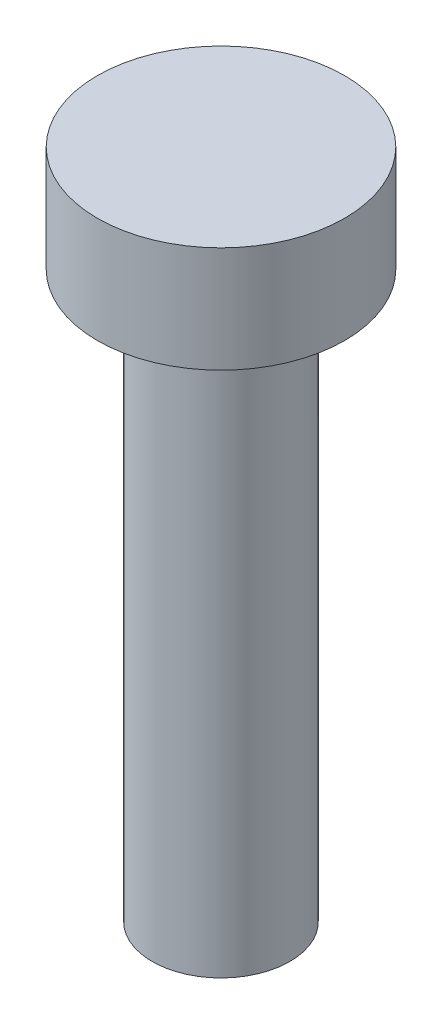
SolidWorks part; units mm, degrees
ref_plane "Front Plane" through (0, 0, 0) normal (0, 0, 1) x (1, 0, 0)
ref_plane "Top Plane" through (0, 0, 0) normal (0, 1, 0) x (1, 0, 0)
ref_plane "Right Plane" through (0, 0, 0) normal (1, 0, 0) x (0, 0, -1)
sketch "Sketch1" plane through (0, 0, 0) normal (0, 1, 0) x (1, 0, 0)
  circle A0 centre (0, 0) radius 3.5
  dimension "D1" = 7
extrude "Boss-Extrude1" add sketch "Sketch1" along normal blind 3
sketch "Sketch2" plane through (0, 0, 0) normal (0, -1, 0) x (1, 0, 0)
  circle A0 centre (0, 0) radius 1.95
  dimension "D1" = 3.9
extrude "Boss-Extrude2" add sketch "Sketch2" along normal blind 16
